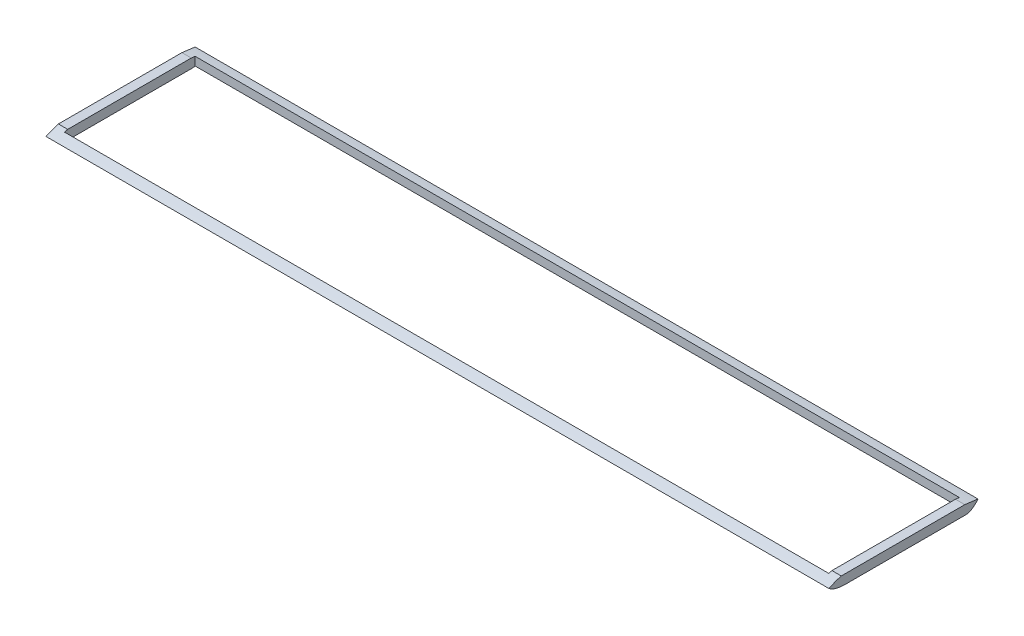
SolidWorks part; units mm, degrees
ref_plane "Front Plane" through (0, 0, 0) normal (0, 0, 1) x (1, 0, 0)
ref_plane "Top Plane" through (0, 0, 0) normal (0, 1, 0) x (1, 0, 0)
ref_plane "Right Plane" through (0, 0, 0) normal (1, 0, 0) x (0, 0, -1)
sketch "Sketch1" plane through (0, 0, 0) normal (0, 1, 0) x (1, 0, 0)
  line L1 (0, 0) -> (-533.4, 0)
  line L2 (0, 0) -> (0, 6.35)
  line L3 (0, 6.35) -> (-533.4, 6.35)
  line L4 (-533.4, 0) -> (-533.4, 6.35)
  line L5 (0, 0) -> (-6.35, 0)
  line L6 (0, 0) -> (0, -95.25)
  line L7 (0, -95.25) -> (-6.35, -95.25)
  line L8 (-6.35, 0) -> (-6.35, -95.25)
  line L9 (-6.35, -95.25) -> (-533.4, -95.25)
  line L10 (-6.35, -95.25) -> (-6.35, -88.9)
  line L11 (-6.35, -88.9) -> (-533.4, -88.9)
  line L12 (-533.4, -95.25) -> (-533.4, -88.9)
  line L13 (-533.4, -88.9) -> (-527.05, -88.9)
  line L14 (-533.4, -88.9) -> (-533.4, 0)
  line L15 (-533.4, 0) -> (-527.05, 0)
  line L16 (-527.05, -88.9) -> (-527.05, 0)
  dimension "D1" = 533.4
  dimension "D2" = 6.35
  dimension "D3" = 101.6
extrude "Boss-Extrude1" add sketch "Sketch1" along normal blind 6.35 contours L11 L16 L1 L14 | L12 L9 L8 L11 | L4 L1 L2 L3 | L1 L8 L7 L6
sketch "Sketch3" plane through (0, 0, 0) normal (1, 0, 0) x (0, 0, -1)
  line L0 (-95.25, 6.35) -> (-95.25, 0) construction
  line L2 (-49.9552, 8.89) -> (-76.968, 8.89) construction
  line L3 (-64.77, 8.89) -> (-64.77, 6.35) construction
  line L4 (-95.25, 6.35) -> (6.35, 6.35) construction
  line L5 (-95.25, 0) -> (6.35, 0) construction
  line L6 (-84.6411, 0) -> (-84.6411, -18.6122)
  line L7 (6.35, 6.35) -> (6.35, 0) construction
  line L8 (-84.6411, -18.6122) -> (-110.0147, -18.6122)
  line L9 (-110.0147, -18.6122) -> (-110.0147, 30.7729)
  line L10 (-110.0147, 30.7729) -> (12.9853, 30.7729)
  line L11 (12.9853, 30.7729) -> (12.9853, -18.6122)
  line L12 (12.9853, -18.6122) -> (-2.571, -18.6122)
  line L13 (-2.571, -18.6122) -> (-2.571, 0)
  spline S0 degree 3 poles (-95.25, 3.175) (-82.3811, 9.2204) (-50.7789, 8.7365) (-10.4222, 7.8511) (6.35, 5.1881) knots 0 0 0 0 0.372908 1 1 1 1
  spline S1 degree 2 poles (-95.25, 3.175) (-91.5443, 0.1144) (-84.6411, 0) knots 0 0 0 1 1 1
  spline S2 degree 2 poles (6.35, 5.1881) (2.0221, -0.2829) (-2.571, 0) knots 0 0 0 1 1 1
  point P22 (0, 0)
  dimension "D1" = 30.48
  dimension "D2" = 2.54
extrude "Cut-Extrude1" cut sketch "Sketch3" against normal through all
